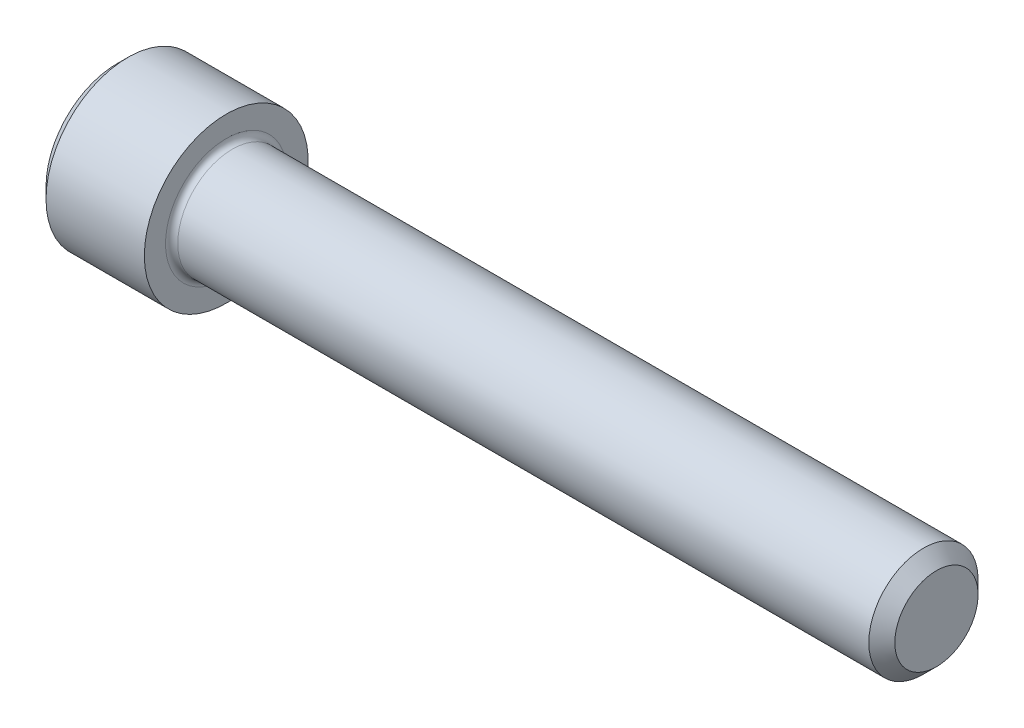
SolidWorks part; units mm, degrees
revolve "Base-Revolve" add sketch "BodySke"
sketch "BodySke" plane through (0, 0, 0) normal (0, 0, 1) x (1, 0, 0)
  line L0 (0, 0) -> (0, 4.1275)
  line L1 (0.635, 4.7625) -> (6.35, 4.7625)
  line L2 (6.35, 4.7625) -> (6.35, 3.175)
  line L3 (6.35, 3.175) -> (46.8693, 3.175)
  line L4 (47.625, 2.4193) -> (47.625, 0)
  line L5 (47.625, 0) -> (0, 0)
  line L6 (-31.75, 0) -> (127, 0) construction
  line L7 (0, 4.1275) -> (0.635, 4.7625)
  line L8 (47.625, 2.4193) -> (46.8693, 3.175)
  line L9 (0, -4.1275) -> (0.635, -4.7625) construction
  line L10 (47.625, -2.4193) -> (46.8693, -3.175) construction
  line L11 (7.62, 9.525) -> (7.62, 3.175) construction
  line L12 (19.05, 9.525) -> (19.05, 3.175) construction
  line L13 (9.525, 9.525) -> (9.525, 3.175) construction
  dimension "Diameter" = 6.35
  dimension "Head_ht" = 6.35
  dimension "Length" = 41.275
  dimension "Body_ch_ang" = 45
  dimension "Head_dia" = 9.525
  dimension "Head_ch_ang" = 45
  dimension "Head_side_ht" = 5.715
  dimension "Minor_dia" = 4.8387
  dimension "Advance" = 1.27
  dimension "Thread_nom" = 28.575
  dimension "Thread_length" = 38.1
cosmetic thread "ThreadCosmetic" [suppressed]
fillet "Fillet1" radius 0.3556 1 edges at (6.35, 0, 3.175)
ref_plane "Plane1" through (0, 0, 0) normal (0, 0, 1) x (1, 0, 0)
ref_plane "Plane2" through (0, 0, 0) normal (0, 1, 0) x (1, 0, 0)
ref_plane "Plane3" through (0, 0, 0) normal (1, 0, 0) x (0, 0, -1)
sketch "Sketch2" plane through (0, 0, 0) normal (0, 0, 1) x (1, 0, 0)
  line L0 (0, 2.3812) -> (3.048, 2.3812)
  line L1 (3.048, 2.3812) -> (4.4228, 0)
  line L2 (-31.75, 0) -> (127, 0) construction
  line L3 (4.4228, 0) -> (0, 0)
  line L4 (0, 0) -> (0, 2.3812)
  line L5 (0, 4.1275) -> (0, -4.1275) construction
  line L6 (0, 0) -> (47.625, 0) construction
  line L7 (6.35, -4.7625) -> (6.35, 4.7625) construction
  dimension "D1" = 2.3813
  dimension "D2" = 60
revolve "Hex-PreBroach" cut sketch "Sketch2" angle 360 about L6
sketch "Sketch3" plane through (0, 0, 0) normal (-1, 0, 0) x (0, 0.5, 0.866)
  line L0 (1.3748, 2.3813) -> (-1.3748, 2.3813)
  line L1 (-1.3748, 2.3813) -> (-2.7496, 0)
  line L2 (1.3748, 2.3813) -> (2.7496, 0)
  line L3 (1.3748, -2.3812) -> (2.7496, 0)
  line L4 (1.3748, -2.3812) -> (-1.3748, -2.3812)
  line L5 (-1.3748, -2.3812) -> (-2.7496, 0)
  dimension "D1" = 2.3813
  dimension "D2" = 2.3813
  dimension "Hex_size" = 4.7625
extrude "Hex" cut sketch "Sketch3" against normal blind 3.048
sketch "Sketch4" plane through (0, 0, 0) normal (-1, 0, 0) x (0, 0, 1)
  line L0 (0, 0) -> (2.8067, 0)
  line L1 (0, 0) -> (6.1484, 3.5498) construction
  line L2 (0, 0) -> (1.4033, 2.4307)
  line L3 (2.3336, 0.614) -> (2.6851, 0.817)
  line L4 (1.6986, 1.7139) -> (2.0501, 1.9169)
  arc A0 (2.3336, 0.614) -> (1.6986, 1.7139) centre (0, 0) ccw
  arc A1 (2.8067, 0) -> (2.6851, 0.817) centre (0, 0) ccw
  arc A2 (1.4033, 2.4307) -> (2.0501, 1.9169) centre (0, 0) cw
  dimension "D1" = 30
  dimension "D2" = 60
  dimension "Spline_p_dim" = 1.27
  dimension "D3" = 0.635
extrude "Spline" [suppressed] cut sketch "Sketch4" against normal blind 3.048
pattern_circular "CirPattern1" [suppressed] count 6 every 60
sketch "Sketch5" plane through (0, 0, 0) normal (0, 0, 1) x (1, 0, 0)
  line L0 (-31.75, 0) -> (127, 0) construction
  line L2 (0, 4.1275) -> (0, -4.1275) construction
  circle A0 centre (2.159, 0) radius 0.5905
  dimension "Drilled_hole_dia" = 1.1811
  dimension "Drilled_hole_loc" = 2.159
extrude "Hole" [suppressed] cut sketch "Sketch5" against normal through all and the other way through all
pattern_circular "Drilled-4" [suppressed] count 2 every 60
pattern_circular "Drilled-6" [suppressed] count 3 every 60
sketch "ThdSchSke" plane through (0, 0, 0) normal (0, 0, 1) x (1, 0, 0)
  line L0 (19.05, -2.4193) -> (18.5209, -3.175)
  line L1 (19.05, -2.4193) -> (19.5791, -3.175)
  line L2 (19.5791, -3.175) -> (19.5791, -3.9687)
  line L3 (-3.175, 0) -> (5.1513, 0) construction
  line L5 (19.5791, -3.9687) -> (18.5209, -3.9687)
  line L6 (18.5209, -3.9687) -> (18.5209, -3.175)
  line L7 (0, 4.1275) -> (0, -4.1275) construction
  dimension "Thread_minor" = 4.8387
  dimension "Diameter" = 6.35
revolve "ThreadSchematic" [suppressed] cut sketch "ThdSchSke" angle 360 about L3
pattern_linear "ThdSchPat" [suppressed]
equation "\"D2@Sketch3\" = \"Hex_size@Sketch3\" / 2"
equation "\"D1@Sketch3\" = \"Hex_size@Sketch3\" / 2"
equation "\"D1@Sketch2\" = \"Hex_size@Sketch3\" / 2"
equation "\"D3@Sketch4\" = \"Spline_p_dim@Sketch4\" / 2"
equation "\"Thread_minor@ThreadCosmetic\"  =  \"Minor_dia@BodySke\""
equation "\"D2@CirPattern1\" = 360 / \"Num_teeth@CirPattern1\""
equation "\"Wall_thickness@Sketch2\" = \"Head_ht@BodySke\" - \"Key_eng@Hex\""
equation "\"Thread_length@ThreadCosmetic\" = ((sgn( (\"Length@BodySke\" - \"Advance@BodySke\" ) - \"Thread_nom@BodySke\" )-1)*( (\"Length@BodySke\" - \"Advance@BodySke\" ) - \"Thread_nom@BodySke\" ))/-2+ \"Thread_nom@BodySke\""
equation "\"Thread_minor@ThdSchSke\" = \"Minor_dia@BodySke\""
equation "\"Diameter@ThdSchSke\" = \"Diameter@BodySke\""
equation "\"Overcut@ThdSchSke\" = \"Diameter@BodySke\" * 1.25"
equation "\"Start@ThdSchSke\" = \"Head_ht@BodySke\" + \"Length@BodySke\" - \"Thread_length@ThreadCosmetic\"  '---Non-countersunk---"
equation "\"Num_threads@ThdSchPat\" = int( \"Thread_length@ThreadCosmetic\" / \"Advance@BodySke\" + 0.999 )  + 1"
equation "\"Advance@ThdSchPat\" = \"Thread_length@ThreadCosmetic\" /  (\"Num_threads@ThdSchPat\" - 1) 'relax it"
equation "\"Num_threads@ThdSchPat\" = \"Num_threads@ThdSchPat\" - sgn( \"Num_threads@ThdSchPat\" - 1) '---chamfered tips only---"
